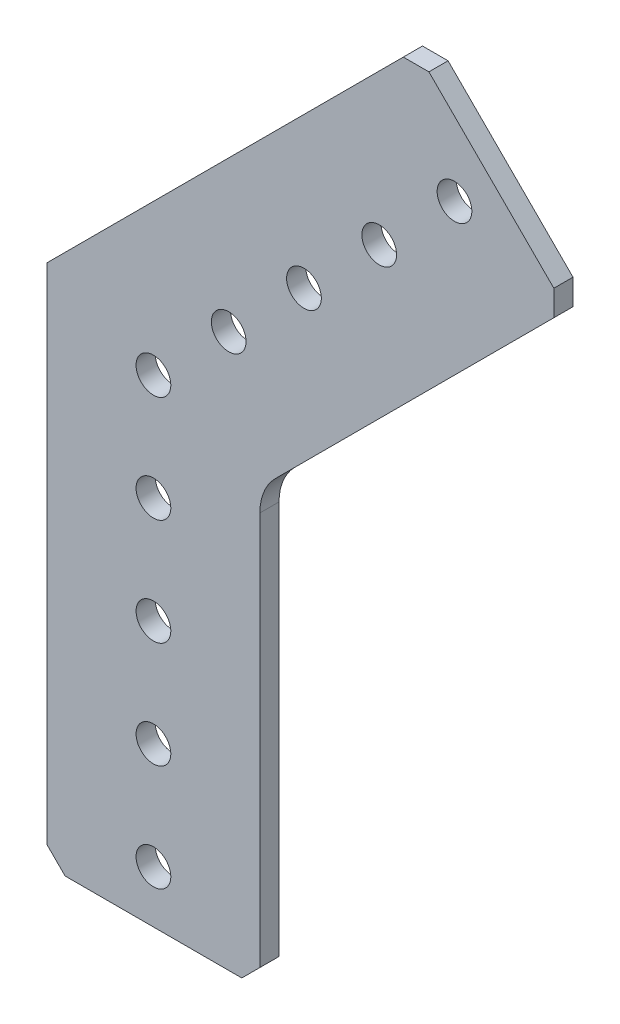
SolidWorks part; units mm, degrees
ref_plane "Front Plane" through (0, 0, 0) normal (0, 0, 1) x (1, 0, 0)
ref_plane "Top Plane" through (0, 0, 0) normal (0, 1, 0) x (1, 0, 0)
ref_plane "Right Plane" through (0, 0, 0) normal (1, 0, 0) x (0, 0, -1)
ref_plane "Plane1" through (0, 0, 2.286) normal (0, 0, 1) x (1, 0, 0)
sketch "Sketch1" plane through (0, 0, 2.286) normal (0, 0, 1) x (1, 0, 0)
  line L0 (32.8677, 47.775) -> (29.8145, 47.775)
  line L1 (29.8145, 47.775) -> (-12.7, 5.2605)
  line L2 (-12.7, 5.2605) -> (-12.7, -54.864)
  line L3 (-12.7, -54.864) -> (-10.541, -57.023)
  line L4 (-10.541, -57.023) -> (10.541, -57.023)
  line L5 (10.541, -57.023) -> (12.7, -54.864)
  line L6 (12.7, -54.864) -> (12.7, -7.8908)
  line L7 (14.5599, -3.4006) -> (47.775, 29.8145)
  line L8 (47.775, 29.8145) -> (47.775, 32.8677)
  line L9 (47.775, 32.8677) -> (32.8677, 47.775)
  circle A0 centre (35.921, 35.921) radius 2.0701
  circle A1 centre (17.9605, 17.9605) radius 2.0701
  circle A2 centre (8.9803, 8.9803) radius 2.0701
  circle A3 centre (26.9408, 26.9408) radius 2.0701
  circle A4 centre (0, -50.8) radius 2.0701
  circle A5 centre (0, -25.4) radius 2.0701
  arc A6 (12.7, -7.8908) -> (14.5599, -3.4006) centre (19.05, -7.8908) cw
  circle A7 centre (0, -12.7) radius 2.0701
  circle A8 centre (0, -38.1) radius 2.0701
  circle A9 centre (0, 0) radius 2.0701
extrude "Boss-Extrude1" add sketch "Sketch1" against normal blind 2.286
